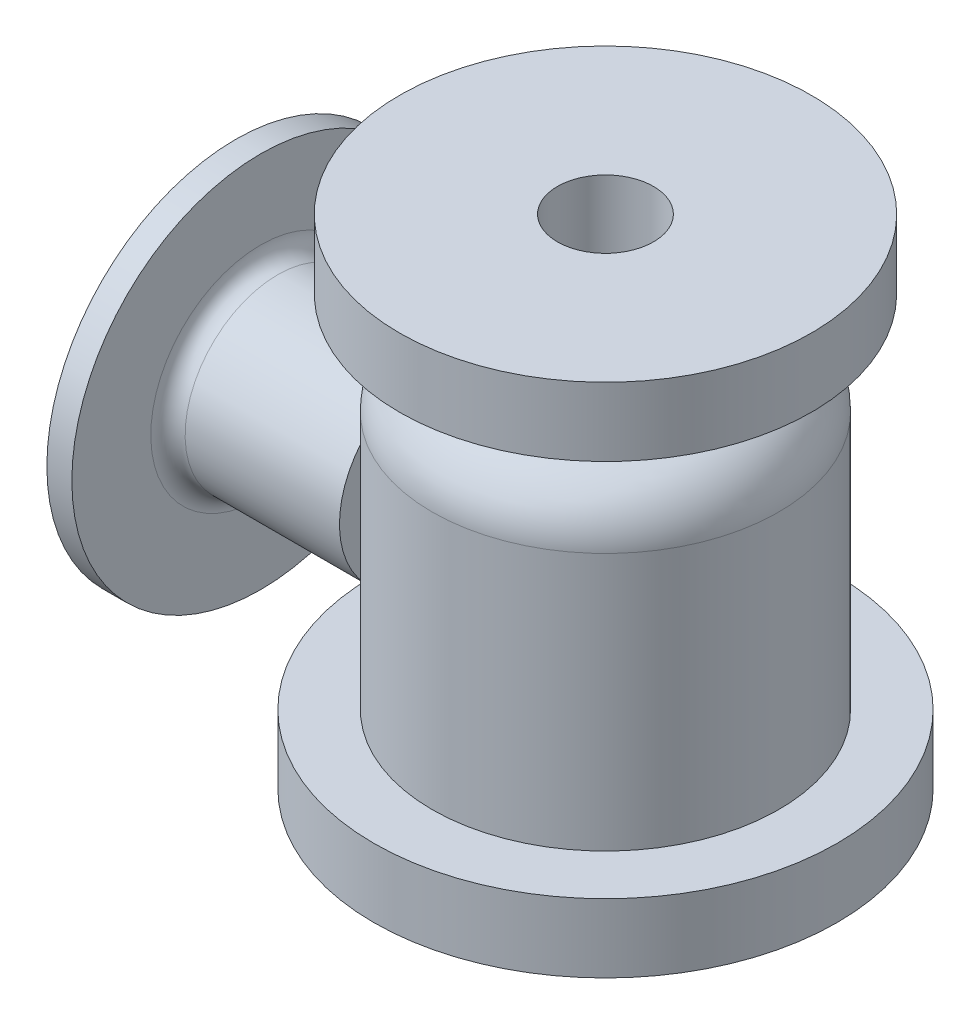
SolidWorks part; units mm, degrees
ref_plane "Front Plane" through (0, 0, 0) normal (0, 0, 1) x (1, 0, 0)
ref_plane "Top Plane" through (0, 0, 0) normal (0, 1, 0) x (1, 0, 0)
ref_plane "Right Plane" through (0, 0, 0) normal (1, 0, 0) x (0, 0, -1)
sketch "Sketch1" plane through (0, 0, 0) normal (0, 0, 1) x (1, 0, 0)
  line L0 (0, 130.5442) -> (0, -139.0411) construction
  line L1 (110, 95) -> (38, 95)
  line L2 (38, 95) -> (38, 64)
  line L3 (38, 64) -> (41, 64)
  line L4 (46, 59) -> (46, 12)
  line L5 (48, 10) -> (57, 10)
  line L6 (57, 10) -> (57, 0)
  line L7 (57, 0) -> (65, 0)
  line L8 (75, -10) -> (75, -166)
  line L9 (75, -166) -> (79, -166)
  line L10 (79, -166) -> (79, -175)
  line L11 (79, -175) -> (125, -175)
  line L12 (125, -175) -> (125, -155)
  line L13 (125, -155) -> (101, -155)
  line L14 (91, -145) -> (91, 5.1729)
  line L16 (65, 31.1729) -> (62, 31.1729)
  line L17 (62, 51.8098) -> (62, 65)
  line L18 (72, 75) -> (110, 75)
  line L19 (110, 75) -> (110, 95)
  line L20 (46, 12) -> (48, 10)
  arc A0 (91, 5.1729) -> (76.5, 28.4913) centre (65, 5.1729) ccw
  arc A1 (46, 59) -> (41, 64) centre (41, 59) ccw
  arc A2 (62, 65) -> (72, 75) centre (72, 65) cw
  arc A3 (76.5, 28.4913) -> (62, 51.8098) centre (88, 51.8098) cw
  arc A4 (65, 0) -> (75, -10) centre (65, -10) cw
  arc A5 (101, -155) -> (91, -145) centre (101, -145) cw
  point P8 (46, 10)
  dimension "D17" = 26
  dimension "D18" = 5
  dimension "D19" = 10
  dimension "D20" = 26
  dimension "D21" = 10
  dimension "D22" = 10
  dimension "D1" = 38
  dimension "D2" = 62
  dimension "D3" = 110
  dimension "D4" = 20
  dimension "D5" = 46
  dimension "D6" = 75
  dimension "D7" = 91
  dimension "D8" = 125
  dimension "D9" = 79
  dimension "D10" = 20
  dimension "D11" = 57
  dimension "D12" = 95
  dimension "D13" = 54
  dimension "D14" = 10
  dimension "D15" = 270
  dimension "D16" = 9
  dimension "D23" = 2
  dimension "D24" = 45
revolve "Revolve-Thin2" add sketch "Sketch1" angle 360 about L0
sketch "Sketch5" plane through (0, 0, 0) normal (0, 0, 1) x (1, 0, 0)
  line L0 (0, -75) -> (-245.1249, -75) construction
  line L1 (-135, -185) -> (135, -185) construction
  line L2 (-215.4916, 35) -> (-215.4916, -37)
  line L3 (-215.4916, -37) -> (-101, -37)
  line L4 (-101, 5.1729) -> (-101, -145) construction
  line L5 (-101, -37) -> (-101, -21)
  line L6 (-101, -21) -> (-190.9348, -21)
  line L7 (-200.9348, -11) -> (-200.9348, 35)
  line L8 (-200.9348, 35) -> (-215.4916, 35)
  arc A0 (-190.9348, -21) -> (-200.9348, -11) centre (-190.9348, -11) cw
  dimension "D5" = 10
  dimension "D1" = 110
  dimension "D2" = 110
  dimension "D3" = 38
  dimension "D4" = 54
revolve "Revolve1" add sketch "Sketch5" angle 360 about L0
